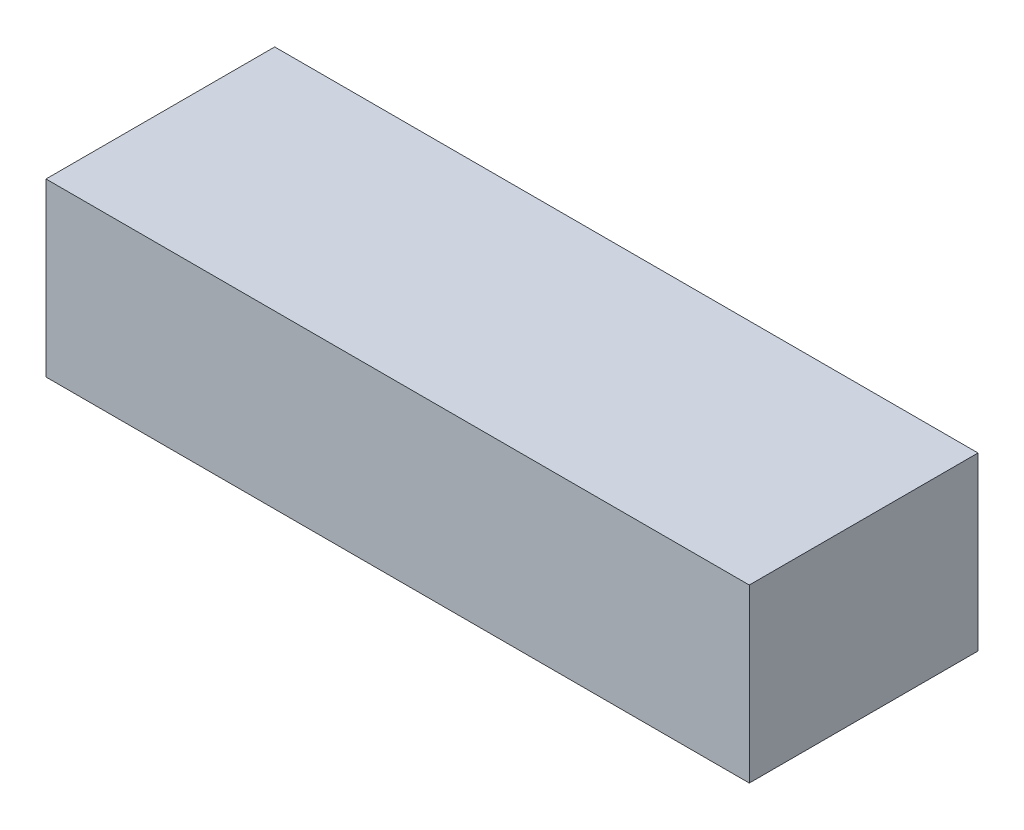
SolidWorks part; units mm, degrees
ref_plane "Płaszczyzna przednia" through (0, 0, 0) normal (0, 0, 1) x (1, 0, 0)
ref_plane "Płaszczyzna górna" through (0, 0, 0) normal (0, 1, 0) x (1, 0, 0)
ref_plane "Płaszczyzna prawa" through (0, 0, 0) normal (1, 0, 0) x (0, 0, -1)
sketch "Szkic1" plane through (0, 0, 0) normal (0, 0, 1) x (1, 0, 0)
  line L1 (0, 0) -> (123, 0)
  line L2 (0, 0) -> (0, 30)
  line L3 (0, 30) -> (123, 30)
  line L4 (123, 0) -> (123, 30)
extrude "Dodanie-wyciągnięcie1" add sketch "Szkic1" along normal blind 40
